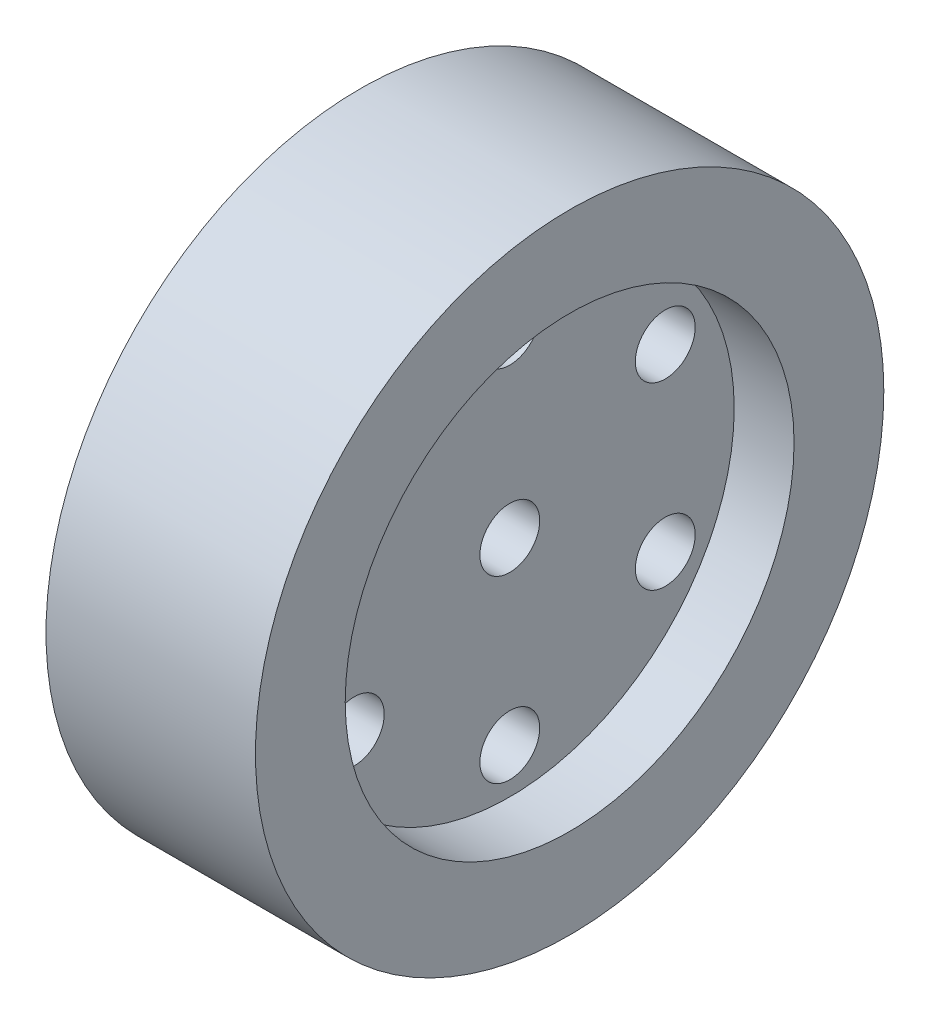
SolidWorks part; units mm, degrees
material "Brass"
ref_plane "Front Plane" through (0, 0, 0) normal (0, 0, 1) x (1, 0, 0)
ref_plane "Top Plane" through (0, 0, 0) normal (0, 1, 0) x (1, 0, 0)
ref_plane "Right Plane" through (0, 0, 0) normal (1, 0, 0) x (0, 0, -1)
sketch "Sketch1" plane through (0, 0, 0) normal (1, 0, 0) x (0, 0, -1)
  circle A0 centre (0, 0) radius 10.5
  dimension "D1" = 21
extrude "Boss-Extrude1" add sketch "Sketch1" along normal blind 7
sketch "Sketch2" plane through (7, 0, 0) normal (1, 0, 0) x (0, 0, -1)
  circle A0 centre (0, 0) radius 7.5
  dimension "D1" = 15
extrude "Cut-Extrude1" cut sketch "Sketch2" against normal blind 2
sketch "Sketch3" plane through (5, 0, 0) normal (1, 0, 0) x (0, 0, -1)
  circle A0 centre (0, 0) radius 6 construction
  circle A1 centre (0, 6) radius 1
  circle A2 centre (0, 0) radius 1
  circle A3 centre (5.1962, 3) radius 1
  circle A4 centre (5.1962, -3) radius 1
  circle A5 centre (0, -6) radius 1
  circle A6 centre (-5.1962, -3) radius 1
  circle A7 centre (-5.1962, 3) radius 1
  point P19 (0, 0)
  dimension "D1" = 12
  dimension "D2" = 2
  dimension "D3" = 2
  dimension "D5" = 6
  dimension "D6" = 6
  dimension "D4" = 6
extrude "Cut-Extrude2" cut sketch "Sketch3" against normal through all
sketch "Sketch4" plane through (0, 0, 0) normal (-1, 0, 0) x (0, 0, 1)
  circle A0 centre (0, 0) radius 9.5
  circle A1 centre (0, 0) radius 2.5
  dimension "D1" = 5
  dimension "D2" = 19
extrude "Cut-Extrude3" cut sketch "Sketch4" against normal blind 2
